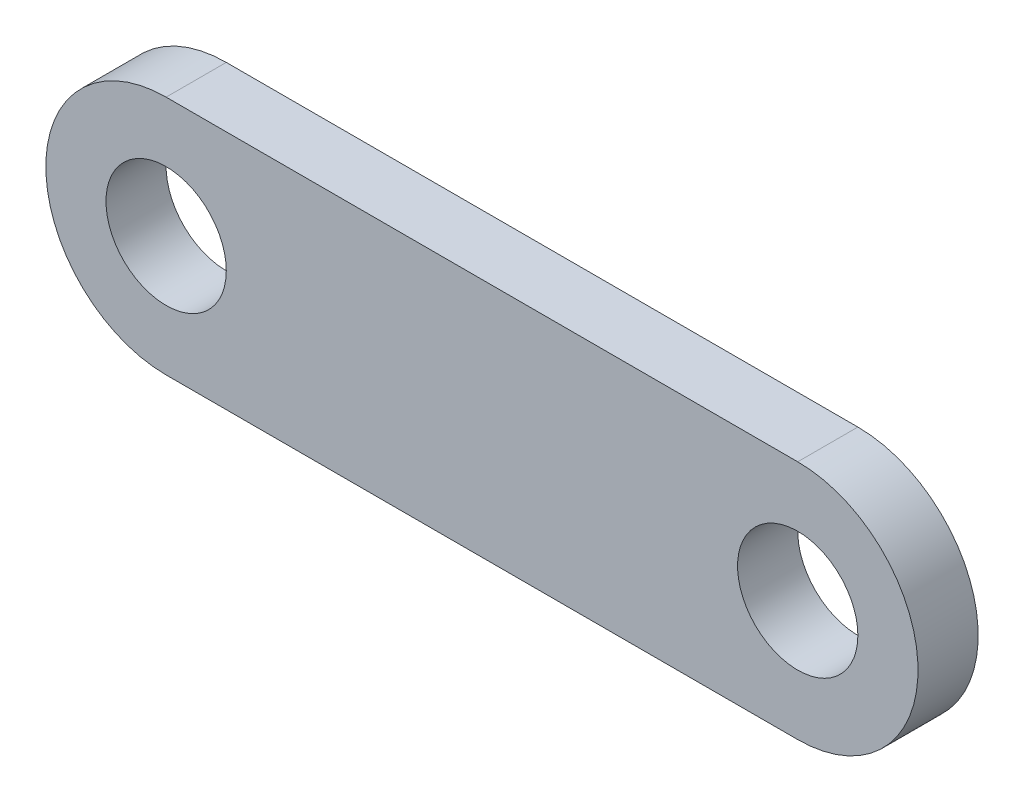
SolidWorks part; units mm, degrees
ref_plane "Front Plane" through (0, 0, 0) normal (0, 0, 1) x (1, 0, 0)
ref_plane "Top Plane" through (0, 0, 0) normal (0, 1, 0) x (1, 0, 0)
ref_plane "Right Plane" through (0, 0, 0) normal (1, 0, 0) x (0, 0, -1)
sketch "Sketch4" plane through (0, 0, 0) normal (0, 0, 1) x (1, 0, 0)
  line L0 (0, 0) -> (-26.67, 0) construction
  line L1 (0, -5.08) -> (-26.67, -5.08)
  line L2 (0, 5.08) -> (-26.67, 5.08)
  arc A0 (0, -5.08) -> (0, 5.08) centre (0, 0) ccw
  arc A1 (-26.67, 5.08) -> (-26.67, -5.08) centre (-26.67, 0) ccw
  circle A2 centre (0, 0) radius 2.54
  circle A3 centre (-26.67, 0) radius 2.54
  point P3 (-13.335, 0)
  dimension "D2" = 5.08
  dimension "D3" = 5.08
  dimension "D4" = 5.08
  dimension "D1" = 26.67
extrude "Boss-Extrude1" add sketch "Sketch4" along normal blind 2.54
